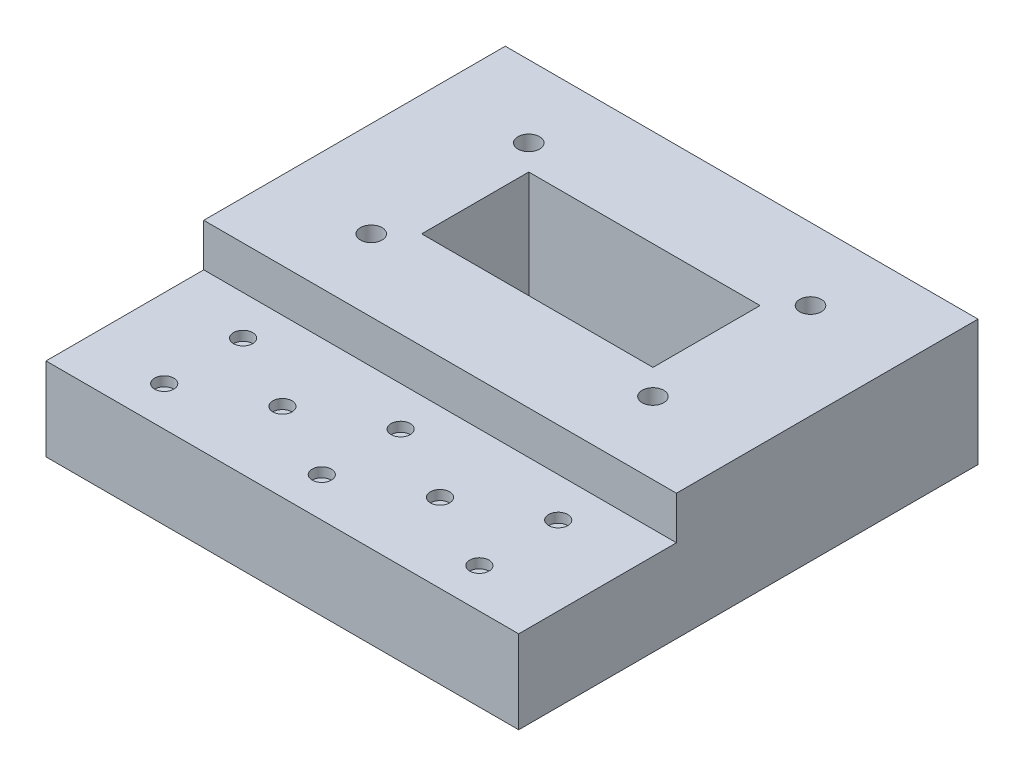
SolidWorks part; units mm, degrees
ref_plane "Front Plane" through (0, 0, 0) normal (0, 0, 1) x (1, 0, 0)
ref_plane "Top Plane" through (0, 0, 0) normal (0, 1, 0) x (1, 0, 0)
ref_plane "Right Plane" through (0, 0, 0) normal (1, 0, 0) x (0, 0, -1)
sketch "Sketch1" plane through (0, 0, 0) normal (0, 1, 0) x (1, 0, 0)
  line L0 (-111.76, 0) -> (-111.76, 9.42)
  line L1 (0, 0) -> (-111.76, 0)
  line L2 (0, 0) -> (0, 75.69)
  line L3 (0, 75.69) -> (-111.76, 75.69)
  line L4 (-111.76, 0) -> (-111.76, 9.42)
  line L5 (-111.76, 9.42) -> (-100.58, 9.42)
  line L7 (-111.76, 16.28) -> (-100.58, 16.28)
  line L8 (-111.76, 16.28) -> (-111.76, 75.69)
  line L9 (0, 0) -> (0, 37.845)
  line L10 (0, 37.845) -> (-111.76, 37.845)
  line L11 (-55.88, 75.69) -> (-55.88, 0)
  line L12 (-111.76, 66.27) -> (-100.58, 66.27)
  line L13 (-111.76, 59.41) -> (-100.58, 59.41)
  line L14 (0, 9.42) -> (-11.18, 9.42)
  line L15 (0, 16.28) -> (-11.18, 16.28)
  line L16 (0, 59.41) -> (-11.18, 59.41)
  line L17 (0, 66.27) -> (-11.18, 66.27)
  arc A0 (-100.58, 9.42) -> (-100.58, 16.28) centre (-100.58, 12.85) ccw
  arc A1 (-100.58, 66.27) -> (-100.58, 59.41) centre (-100.58, 62.84) cw
  arc A2 (-11.18, 9.42) -> (-11.18, 16.28) centre (-11.18, 12.85) cw
  arc A3 (-11.18, 66.27) -> (-11.18, 59.41) centre (-11.18, 62.84) ccw
  dimension "D1" = 111.76
  dimension "D2" = 75.69
sketch "Sketch2" plane through (0, 0, 0) normal (0, 1, 0) x (1, 0, 0)
  line L0 (-55.88, 0) -> (-55.88, 75.69)
  line L1 (-111.76, 0) -> (-121.76, 0)
  line L2 (-111.76, 0) -> (-111.76, -10)
  line L3 (-111.76, -10) -> (-121.76, -10)
  line L4 (-121.76, 0) -> (-121.76, -10)
  line L5 (0, 75.69) -> (10, 75.69)
  line L6 (0, 75.69) -> (0, 85.69)
  line L7 (0, 85.69) -> (10, 85.69)
  line L8 (10, 75.69) -> (10, 85.69)
  line L9 (-111.76, 37.845) -> (0, 37.845)
  circle A0 centre (-100.58, 12.85) radius 3.43
  circle A1 centre (-100.58, 12.85) radius 8
  circle A2 centre (-100.58, 62.84) radius 8
  circle A3 centre (-11.18, 12.85) radius 8
  circle A4 centre (-11.18, 62.84) radius 8
  dimension "D1" = 10
  dimension "D2" = 10
  dimension "D3" = 10
  dimension "D4" = 10
sketch "Sketch3" plane through (0, 0, 0) normal (0, 1, 0) x (1, 0, 0)
  line L0 (-100.58, 54.84) -> (-92.58, 54.84)
  line L1 (-121.76, -10) -> (-108.58, -10)
  line L2 (-121.76, -10) -> (-121.76, 12.85)
  line L5 (-108.58, -10) -> (-11.18, -10)
  line L9 (10, 85.69) -> (-3.18, 85.69)
  line L10 (10, 85.69) -> (10, 62.84)
  line L14 (10, 62.84) -> (10, -10)
  line L15 (10, -10) -> (-3.18, -10)
  line L19 (-11.18, -10) -> (-3.18, -10)
  line L22 (-121.76, 12.85) -> (-121.76, 62.84)
  line L26 (-121.76, 62.84) -> (-121.76, 85.69)
  line L27 (-121.76, 85.69) -> (-108.58, 85.69)
  line L29 (-108.58, 85.69) -> (-11.18, 85.69)
  line L35 (-11.18, 85.69) -> (-3.18, 85.69)
  line L37 (-92.58, 62.84) -> (-92.58, 54.84)
  line L38 (-19.18, 12.85) -> (-19.18, 20.85)
  line L39 (-11.18, 20.85) -> (-19.18, 20.85)
  line L41 (-92.58, 54.84) -> (-19.18, 54.84)
  line L42 (-92.58, 54.84) -> (-92.58, 20.85)
  line L43 (-92.58, 20.85) -> (-19.18, 20.85)
  line L44 (-19.18, 54.84) -> (-19.18, 20.85)
  circle A1 centre (-11.18, 12.85) radius 8 construction
  circle A3 centre (-100.58, 62.84) radius 8 construction
  circle A8 centre (-100.58, 62.84) radius 3.43
  circle A9 centre (-11.18, 62.84) radius 3.43
  circle A10 centre (-11.18, 12.85) radius 3.43
  circle A11 centre (-100.58, 12.85) radius 3.43
sketch "Sketch4" plane through (0, 0, 0) normal (0, 1, 0) x (1, 0, 0)
  line L0 (-108.58, 62.84) -> (-108.58, 70.84)
  line L1 (-108.58, 12.85) -> (-108.58, 4.85)
  line L2 (-108.58, 70.84) -> (-121.76, 70.84)
  line L3 (-108.58, 70.84) -> (-108.58, 85.69)
  line L4 (-108.58, 85.69) -> (-121.76, 85.69)
  line L5 (-121.76, 70.84) -> (-121.76, 85.69)
  line L6 (-55.88, 0) -> (-55.88, 75.69)
  line L7 (-108.58, 4.85) -> (-121.76, 4.85)
  line L8 (-108.58, 4.85) -> (-108.58, -10)
  line L9 (-108.58, -10) -> (-121.76, -10)
  line L10 (-121.76, 4.85) -> (-121.76, -10)
  line L11 (0, 0) -> (-111.76, 0) construction
  line L12 (10, 4.85) -> (10, -10)
  line L13 (-3.18, -10) -> (10, -10)
  line L14 (-3.18, 4.85) -> (-3.18, -10)
  line L15 (-3.18, 4.85) -> (10, 4.85)
  line L16 (-3.18, 70.84) -> (10, 70.84)
  line L17 (10, 70.84) -> (10, 85.69)
  line L18 (-3.18, 85.69) -> (10, 85.69)
  line L19 (-3.18, 70.84) -> (-3.18, 85.69)
  circle A0 centre (-100.58, 62.84) radius 8 construction
  circle A1 centre (-100.58, 12.85) radius 8 construction
sketch "Sketch8" plane through (0, 0, 0) normal (0, 1, 0) x (1, 0, 0)
  line L1 (-92.58, 20.85) -> (-19.18, 20.85)
  line L2 (-92.58, 20.85) -> (-92.58, 54.84)
  line L3 (-92.58, 54.84) -> (-19.18, 54.84)
  line L4 (-19.18, 20.85) -> (-19.18, 54.84)
  line L5 (-121.76, 85.69) -> (10, 85.69)
  line L6 (-121.76, 85.69) -> (-121.76, -10)
  line L7 (-121.76, -10) -> (10, -10)
  line L8 (10, 85.69) -> (10, -10)
  circle A0 centre (-100.58, 12.85) radius 3.43
  circle A1 centre (-100.58, 62.84) radius 3.43
  circle A2 centre (-11.18, 62.84) radius 3.43
  circle A3 centre (-11.18, 12.85) radius 3.43
extrude "Boss-Extrude4" add sketch "Sketch8" along normal blind 40
sketch "Sketch9" plane through (0, 0, 0) normal (0, -1, 0) x (1, 0, 0)
  circle A0 centre (-100.58, -12.85) radius 8
  circle A1 centre (-11.18, -12.85) radius 8
  circle A2 centre (-11.18, -62.84) radius 8
  circle A3 centre (-100.58, -62.84) radius 8
extrude "Cut-Extrude2" cut sketch "Sketch9" against normal blind 8
sketch "Sketch10" plane through (0, 0, 0) normal (0, -1, 0) x (1, 0, 0)
  line L1 (-121.76, 10) -> (10, 10)
  line L2 (-121.76, 10) -> (-121.76, 60)
  line L3 (-121.76, 60) -> (10, 60)
  line L4 (10, 10) -> (10, 60)
  line L5 (-121.76, 60) -> (-108.58, 60)
  line L6 (-121.76, 60) -> (-121.76, 45.15)
  line L7 (-121.76, 45.15) -> (-108.58, 45.15)
  line L8 (-108.58, 60) -> (-108.58, 45.15)
  dimension "D1" = 50
  dimension "D2" = 13.18
  dimension "D3" = 14.85
sketch "Sketch11" plane through (0, 40, 0) normal (0, 1, 0) x (1, 0, 0)
  line L1 (-121.76, -60) -> (10, -60)
  line L2 (-121.76, -60) -> (-121.76, -10)
  line L3 (-121.76, -10) -> (10, -10)
  line L4 (10, -60) -> (10, -10)
sketch "Sketch12" plane through (0, 0, 0) normal (0, -1, 0) x (1, 0, 0)
  line L1 (-121.76, 10) -> (-130.88, 10)
  line L2 (-130.88, 10) -> (19.12, 10)
  line L3 (19.12, 10) -> (19.12, -85.69)
  line L4 (19.12, -85.69) -> (-130.88, -85.69)
  line L5 (-130.88, -85.69) -> (-130.88, 10)
  line M9 (-121.76, 10) -> (-121.76, -85.69)
  line M11 (10, -85.69) -> (10, 10)
extrude "Boss-Extrude5" add sketch "Sketch12" against normal up to surface (40 mm away) contours L5 L4 L1 M9 | L4 L3 L2 M11 up to face at (-11.18, 40, -59.41)
sketch "Sketch13" plane through (0, 0, 0) normal (0, -1, 0) x (1, 0, 0)
  line L1 (-130.88, 10) -> (19.12, 10)
  line L2 (-130.88, 10) -> (-130.88, 60.05)
  line L3 (-130.88, 60.05) -> (19.12, 60.05)
  line L4 (19.12, 10) -> (19.12, 60.05)
  dimension "D1" = 50.05
extrude "Boss-Extrude6" add sketch "Sketch13" against normal blind 26.38
sketch "Sketch14" plane through (0, 26.38, 0) normal (0, 1, 0) x (1, 0, 0)
  line L0 (-130.88, -60.05) -> (-105.88, -60.05)
  line L1 (-130.88, -60.05) -> (19.12, -60.05)
  line L2 (-130.88, -60.05) -> (-130.88, -10)
  line L3 (-130.88, -10) -> (19.12, -10)
  line L4 (19.12, -60.05) -> (19.12, -10)
  line L5 (-105.88, -60.05) -> (-80.88, -60.05)
  line L6 (-80.88, -60.05) -> (-55.88, -60.05)
  line L7 (-55.88, -60.05) -> (-30.88, -60.05)
  line L8 (-30.88, -60.05) -> (-5.88, -60.05)
  line L9 (-5.88, -60.05) -> (19.12, -60.05)
  line L10 (19.12, -35.025) -> (-130.88, -35.025)
  line L11 (-5.88, -60.05) -> (-5.88, -35.025)
  line L12 (-30.88, -60.05) -> (-30.88, -35.025)
  line L13 (-55.88, -60.05) -> (-55.88, -35.025)
  line L14 (-5.88, -35.025) -> (-5.88, -10)
  line L15 (-30.88, -35.025) -> (-30.88, -10)
  line L16 (-55.88, -35.025) -> (-55.88, -10)
  circle A0 centre (-30.88, -35.025) radius 3.05
  circle A3 centre (-5.88, -47.5375) radius 3.05
  circle A4 centre (-5.88, -22.5125) radius 3.05
  circle A5 centre (-55.88, -22.5125) radius 3.05
  circle A6 centre (-55.88, -47.5375) radius 3.05
  circle A7 centre (-105.88, -22.5125) radius 3.05
  circle A8 centre (-105.88, -47.5375) radius 3.05
  circle A9 centre (-80.88, -35.025) radius 3.05
extrude "Cut-Extrude3" cut sketch "Sketch14" against normal blind 3.05 contours A7 | A8 | A9 L10 | A9 L10 | L16 A5 | L16 A5 | L13 A6 | L13 A6 | L10 A0 L12 | L12 A0 L10 | L10 A0 L15 | L15 A0 L10 | L14 A4 | L14 A4 | L11 A3 | L11 A3
